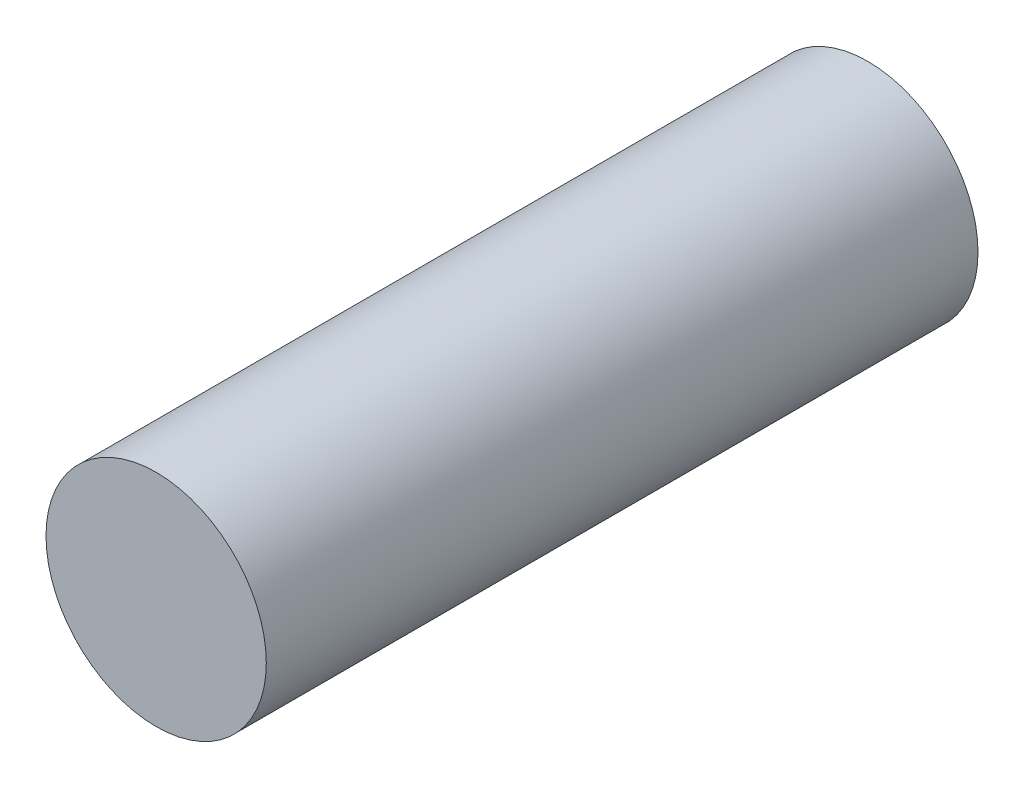
SolidWorks part; units mm, degrees
material "AISI 304"
ref_plane "Front Plane" through (0, 0, 0) normal (0, 0, 1) x (1, 0, 0)
ref_plane "Top Plane" through (0, 0, 0) normal (0, 1, 0) x (1, 0, 0)
ref_plane "Right Plane" through (0, 0, 0) normal (1, 0, 0) x (0, 0, -1)
sketch "Sketch1" plane through (0, 0, 0) normal (1, 0, 0) x (0, 0, -1)
  line L0 (-52.5, 0) -> (52.5, 0)
  line L1 (-52.5, -16.25) -> (-52.5, 16.25) construction
  line L2 (-52.5, 16.25) -> (52.5, 16.25)
  line L3 (52.5, 16.25) -> (52.5, -16.25) construction
  line L4 (-52.5, -16.25) -> (52.5, -16.25) construction
  line L5 (0, 0) -> (0, 16.25) construction
  line L6 (52.5, 0) -> (52.5, 16.25)
  line L7 (-52.5, 0) -> (-52.5, 16.25)
  line L8 (0, 0) -> (52.5, 0) construction
  point P9 (-52.5, 0)
  dimension "D1" = 32.5
  dimension "D2" = 105
revolve "Revolve1" add sketch "Sketch1" angle 360 about L8
